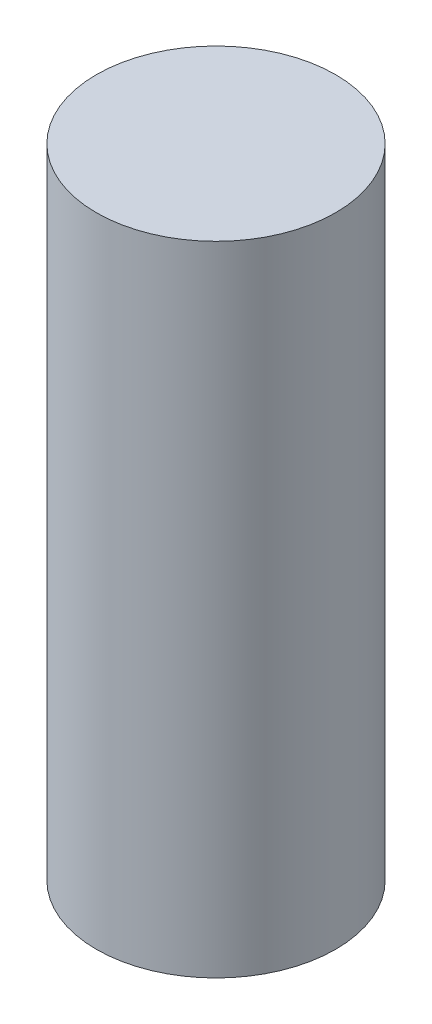
SolidWorks part; units mm, degrees
ref_plane "Front Plane" through (0, 0, 0) normal (0, 0, 1) x (1, 0, 0)
ref_plane "Top Plane" through (0, 0, 0) normal (0, 1, 0) x (1, 0, 0)
ref_plane "Right Plane" through (0, 0, 0) normal (1, 0, 0) x (0, 0, -1)
sketch "Sketch1" plane through (0, 0, 0) normal (0, 1, 0) x (1, 0, 0)
  circle A0 centre (0, 0) radius 6
  dimension "D1" = 12
extrude "Boss-Extrude1" add sketch "Sketch1" along normal blind 32
